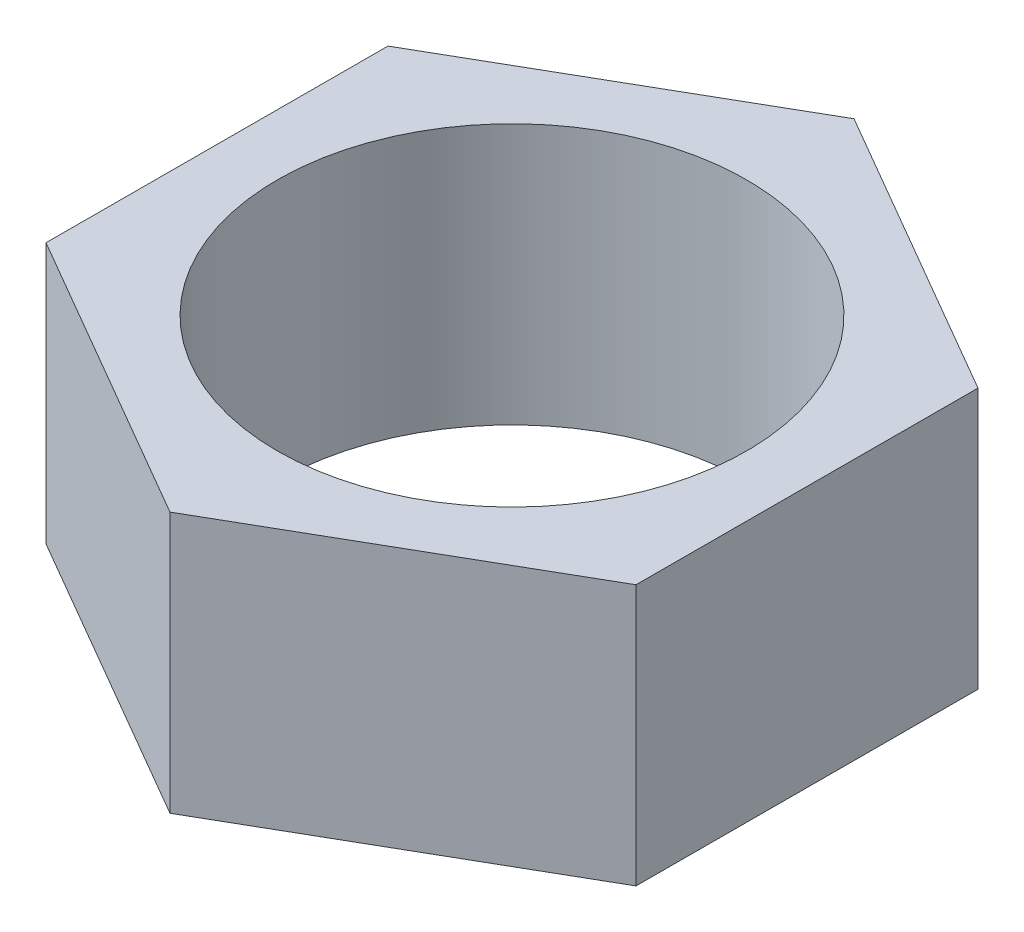
SolidWorks part; units mm, degrees
ref_plane "Front Plane" through (0, 0, 0) normal (0, 0, 1) x (1, 0, 0)
ref_plane "Top Plane" through (0, 0, 0) normal (0, 1, 0) x (1, 0, 0)
ref_plane "Right Plane" through (0, 0, 0) normal (1, 0, 0) x (0, 0, -1)
sketch "Sketch3" plane through (0, 0, 0) normal (0, 1, 0) x (1, 0, 0)
  line L2 (15.8468, -9.1924) -> (15.8843, 9.1276)
  line L3 (15.8843, 9.1276) -> (0.0374, 18.32)
  line L4 (0.0374, 18.32) -> (-15.8468, 9.1924)
  line L5 (-15.8468, 9.1924) -> (-15.8843, -9.1276)
  line L6 (-15.8843, -9.1276) -> (-0.0374, -18.32)
  line L7 (-0.0374, -18.32) -> (15.8468, -9.1924)
  circle A0 centre (0, 0) radius 15.8656 construction
  circle A1 centre (0, 0) radius 12.6
  dimension "D2" = 25.2
  dimension "D1" = 36.64
extrude "Boss-Extrude1" add sketch "Sketch3" along normal mid plane 14
